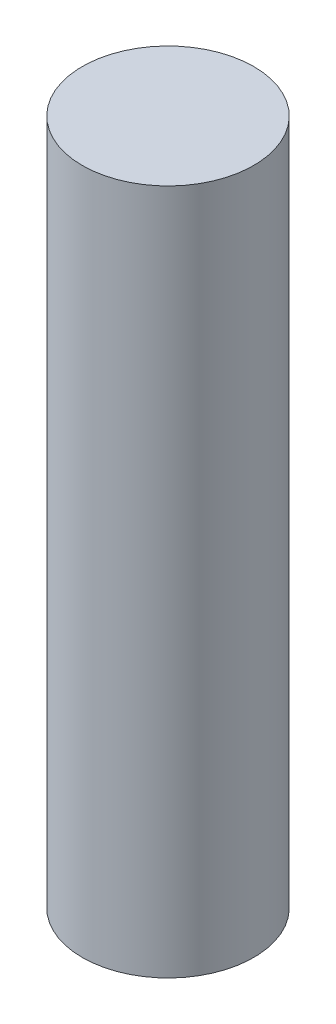
SolidWorks part; units mm, degrees
ref_plane "Front Plane" through (0, 0, 0) normal (0, 0, 1) x (1, 0, 0)
ref_plane "Top Plane" through (0, 0, 0) normal (0, 1, 0) x (1, 0, 0)
ref_plane "Right Plane" through (0, 0, 0) normal (1, 0, 0) x (0, 0, -1)
sketch "Sketch1" plane through (0, 0, 0) normal (0, 1, 0) x (1, 0, 0)
  circle A0 centre (0, 0) radius 0.7937
  dimension "D1" = 1.5875
extrude "Boss-Extrude1" add sketch "Sketch1" along normal blind 6.35
